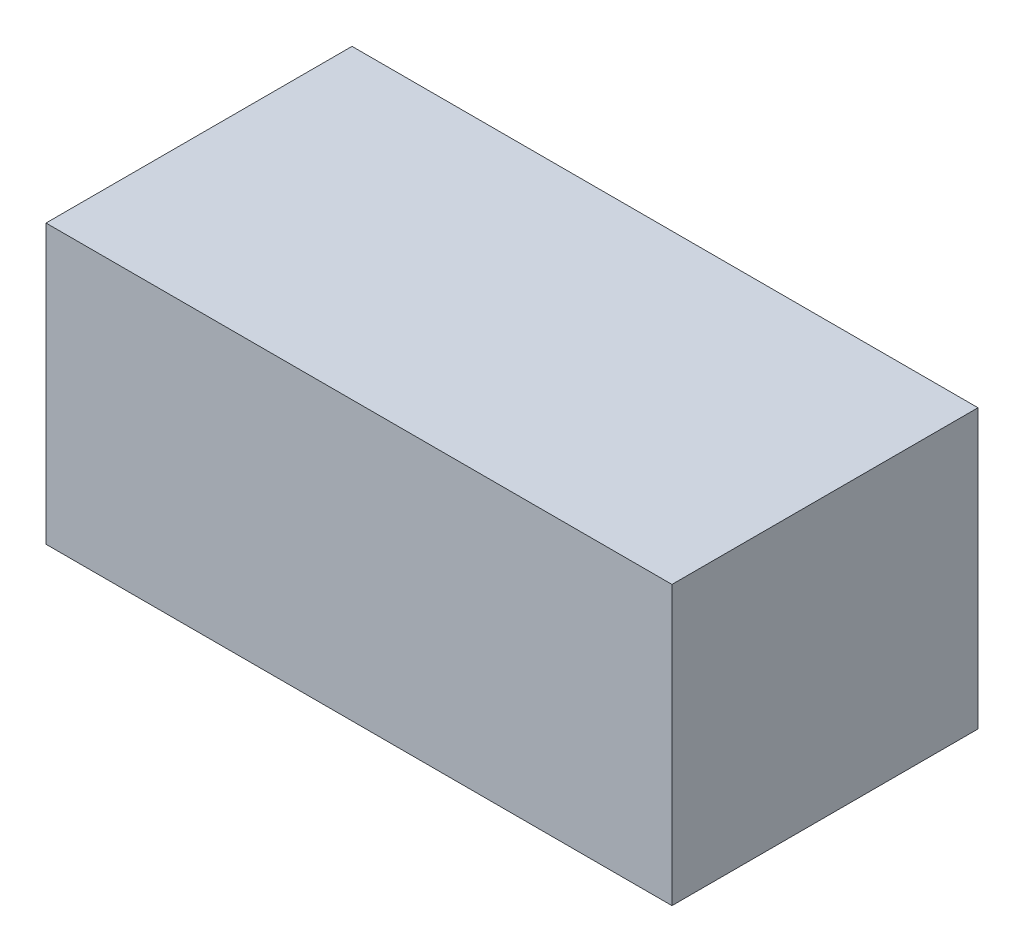
SolidWorks part; units mm, degrees
ref_plane "Front Plane" through (0, 0, 0) normal (0, 0, 1) x (1, 0, 0)
ref_plane "Top Plane" through (0, 0, 0) normal (0, 1, 0) x (1, 0, 0)
ref_plane "Right Plane" through (0, 0, 0) normal (1, 0, 0) x (0, 0, -1)
sketch "Sketch1" plane through (0, 0, 0) normal (0, 1, 0) x (1, 0, 0)
  line L1 (-23.1761, 9.4948) -> (21.8239, 9.4948)
  line L2 (-23.1761, 9.4948) -> (-23.1761, -12.5052)
  line L3 (-23.1761, -12.5052) -> (21.8239, -12.5052)
  line L4 (21.8239, 9.4948) -> (21.8239, -12.5052)
  dimension "D1" = 45
  dimension "D2" = 22
extrude "Boss-Extrude1" add sketch "Sketch1" along normal blind 20
sketch "Sketch2" plane through (0, 0, 0) normal (0, -1, 0) x (1, 0, 0)
  line L1 (-22.6761, 12.0052) -> (21.3239, 12.0052)
  line L2 (-22.6761, 12.0052) -> (-22.6761, -8.9948)
  line L3 (-22.6761, -8.9948) -> (21.3239, -8.9948)
  line L4 (21.3239, 12.0052) -> (21.3239, -8.9948)
  dimension "D1" = 21
  dimension "D2" = 0.5
  dimension "D3" = 44
  dimension "D4" = 0.5
extrude "Cut-Extrude1" cut sketch "Sketch2" against normal blind 18
sketch "Sketch3" plane through (21.8239, 0, 0) normal (1, 0, 0) x (0, 0, -1)
  line L0 (-12.5052, 0) -> (9.4948, 0) construction
  line L1 (8.4948, 0) -> (-11.5052, 0)
  line L2 (8.4948, 0) -> (8.4948, 19.367)
  line L3 (8.4948, 19.367) -> (-11.5052, 19.367)
  line L4 (-11.5052, 0) -> (-11.5052, 19.367)
  dimension "D1" = 1
  dimension "D2" = 1
